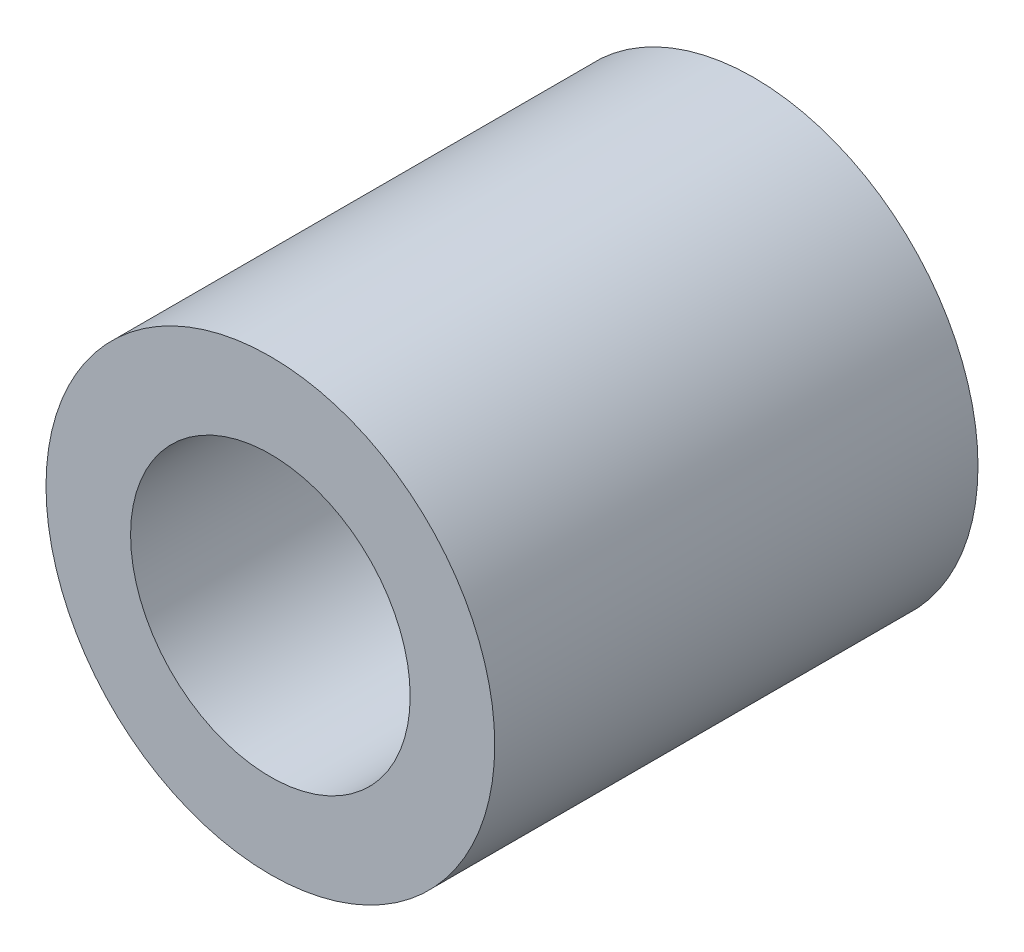
SolidWorks part; units mm, degrees
ref_plane "Alzado" through (0, 0, 0) normal (0, 0, 1) x (1, 0, 0)
ref_plane "Planta" through (0, 0, 0) normal (0, 1, 0) x (1, 0, 0)
ref_plane "Vista lateral" through (0, 0, 0) normal (1, 0, 0) x (0, 0, -1)
sketch "Croquis1" plane through (0, 0, 0) normal (0, 0, 1) x (1, 0, 0)
  circle A0 centre (0, 0) radius 6.5
  circle A1 centre (0, 0) radius 4.05
  dimension "D1" = 13
  dimension "D2" = 8.1
extrude "Saliente-Extruir1" add sketch "Croquis1" along normal blind 14
